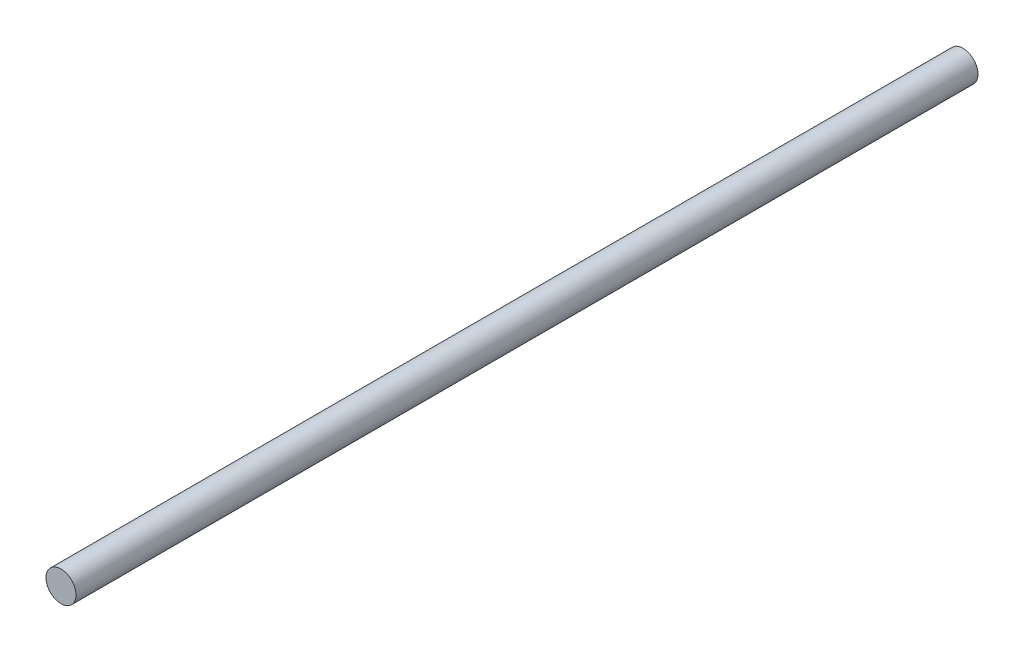
SolidWorks part; units mm, degrees
ref_plane "Front Plane" through (0, 0, 0) normal (0, 0, 1) x (1, 0, 0)
ref_plane "Top Plane" through (0, 0, 0) normal (0, 1, 0) x (1, 0, 0)
ref_plane "Right Plane" through (0, 0, 0) normal (1, 0, 0) x (0, 0, -1)
sketch "Sketch1" plane through (0, 0, 0) normal (0, 0, 1) x (1, 0, 0)
  circle A0 centre (0, 0) radius 12.7
extrude "Boss-Extrude1" add sketch "Sketch1" along normal blind 762
